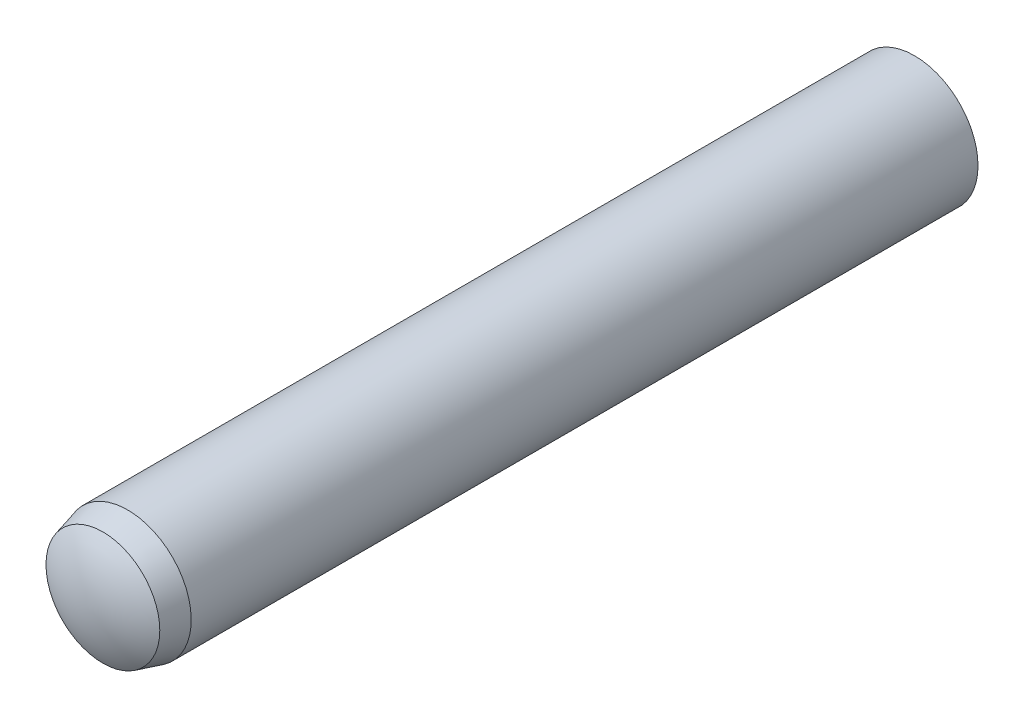
SolidWorks part; units mm, degrees
ref_plane "Front Plane" through (0, 0, 0) normal (0, 0, 1) x (1, 0, 0)
ref_plane "Top Plane" through (0, 0, 0) normal (0, 1, 0) x (1, 0, 0)
ref_plane "Right Plane" through (0, 0, 0) normal (1, 0, 0) x (0, 0, -1)
sketch "Sketch1" plane through (0, 0, 0) normal (0, 0, 1) x (1, 0, 0)
  circle A0 centre (0, 0) radius 1.5
  point P3 (0, 1.5)
  dimension "Diameter" = 3
sketch "Sketch2" plane through (0, 0, 0) normal (1, 0, 0) x (0, 0, -1)
  line L0 (-10, 0) -> (10, 0) construction
  line L1 (-10, 0) -> (-10, 1.5) construction
  line L2 (-10, 1.5) -> (10, 1.5)
  line L3 (10, 1.5) -> (10, 0) construction
  line L4 (-9.61, 1.3432) -> (-9.025, 1.5)
  arc A0 (-10, 0) -> (-9.61, 1.3432) centre (-7.4918, 0) cw
  arc A1 (10, 0) -> (9.55, 1.5) centre (7.275, 0) ccw
  point P2 (0, 0)
  point P11 (-7, 0)
  point P13 (7, 0)
  dimension "Length" = 20
  dimension "D1" = 15
  dimension "D2" = 0.45
  dimension "D3" = 0.975
  dimension "D4" = 0.585
  dimension "D5" = 3
  dimension "D6" = 3
sketch "Sketch3" plane through (0, 0, 0) normal (1, 0, 0) x (0, 0, -1)
  line L0 (-10, 0) -> (10, 0) construction
  line L1 (-9.61, 1.3432) -> (-9.025, 1.5) construction
  line L2 (-10, 0) -> (10, 0)
  line L3 (-9.61, 1.3432) -> (-9.025, 1.5)
  line L4 (-9.025, 1.5) -> (9.55, 1.5)
  arc A0 (10, 0) -> (9.55, 1.5) centre (7.275, 0) ccw construction
  arc A1 (-9.61, 1.3432) -> (-10, 0) centre (-7.4918, 0) ccw construction
  arc A2 (10, 0) -> (9.55, 1.5) centre (7.275, 0) ccw
  arc A3 (-9.61, 1.3432) -> (-10, 0) centre (-7.4918, 0) ccw
revolve "Revolve1" add sketch "Sketch3" angle 360 about L2
equation "\"D2@Sketch2\" = \"Diameter@Sketch1\" * .15"
equation "\"D3@Sketch2\" = \"Diameter@Sketch1\" * .325"
equation "\"D4@Sketch2\" = \"D3@Sketch2\" * .6"
equation "\"D5@Sketch2\"=\"Diameter@Sketch1\""
equation "\"D6@Sketch2\"=\"D5@sketch2\""
